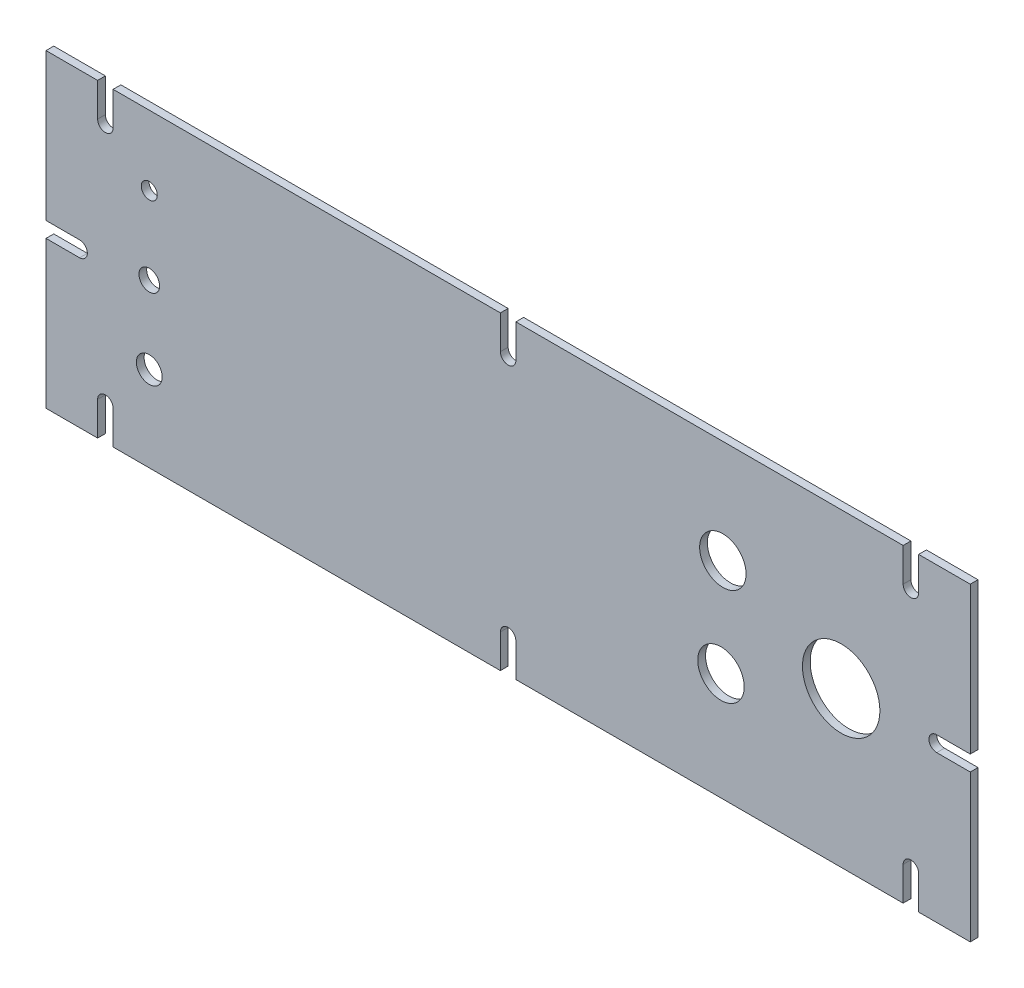
SolidWorks part; units mm, degrees
ref_plane "Front Plane" through (0, 0, 0) normal (0, 0, 1) x (1, 0, 0)
ref_plane "Top Plane" through (0, 0, 0) normal (0, 1, 0) x (1, 0, 0)
ref_plane "Right Plane" through (0, 0, 0) normal (1, 0, 0) x (0, 0, -1)
sketch "Sketch1" plane through (0, 0, 0) normal (0, 0, 1) x (1, 0, 0)
  line L1 (-179, 60) -> (179, 60)
  line L2 (-179, 60) -> (-179, -60)
  line L3 (-179, -60) -> (179, -60)
  line L4 (179, 60) -> (179, -60)
  line L5 (-179, 60) -> (179, -60) construction
  line L6 (-179, -60) -> (179, 60) construction
  point P0 (0, 0)
  dimension "D1" = 120
  dimension "D2" = 358
extrude "Boss-Extrude1" add sketch "Sketch1" along normal blind 3
sketch "Sketch2" plane through (0, 0, 3) normal (0, 0, 1) x (1, 0, 0)
  line L0 (179, 0) -> (88.5, 0) construction
  line L1 (179, -60) -> (179, 60) construction
  circle A0 centre (129, 0) radius 15
  circle A1 centre (83.1742, 20) radius 9
  circle A3 centre (82.4529, -18.2615) radius 9
  point P13 (128.9994, -0.0015)
  dimension "D1" = 30
  dimension "D3" = 18
  dimension "D6" = 2
  dimension "D2" = 50
  dimension "D4" = 20
  dimension "D5" = 50
extrude "Cut-Extrude1" cut sketch "Sketch2" against normal blind 10
sketch "Sketch3" plane through (0, 0, 3) normal (0, 0, 1) x (1, 0, 0)
  line L0 (-179, 60) -> (-179, -60) construction
  line L1 (362, 63) -> (312, 63) construction
  circle A0 centre (-139, 33) radius 3.1
  circle A1 centre (-139, 3) radius 4
  circle A2 centre (-139, -27) radius 5
  dimension "D1" = 6.2
  dimension "D4" = 8
  dimension "D5" = 10
  dimension "D2" = 40
  dimension "D3" = 30
  dimension "D6" = 30
  dimension "D7" = 30
extrude "Cut-Extrude2" cut sketch "Sketch3" against normal blind 10
sketch "Sketch4" plane through (0, 0, 3) normal (0, 0, 1) x (1, 0, 0)
  line L0 (-159, -60) -> (-159, -47)
  line L1 (-179, -60) -> (179, -60) construction
  line L2 (-153, -47) -> (-153, -60)
  line L3 (-179, 60) -> (-179, -60) construction
  line L4 (0, 60) -> (0, -60) construction
  line L5 (0, -60) -> (0, 60) construction
  line L6 (0, 0) -> (37.5832, 0) construction
  line L7 (-153, 47) -> (-153, 60)
  line L8 (-159, 60) -> (-159, 47)
  line L9 (159, 60) -> (159, 47)
  line L10 (153, 47) -> (153, 60)
  line L11 (153, -47) -> (153, -60)
  line L12 (159, -60) -> (159, -47)
  line L13 (-179, 0) -> (179, 0) construction
  line L14 (179, -60) -> (179, 60) construction
  line L15 (-179, 3) -> (-166, 3)
  line L16 (-166, -3) -> (-179, -3)
  line L17 (-3, -60) -> (-3, -47)
  line L18 (3, -47) -> (3, -60)
  line L19 (166, -3) -> (179, -3)
  line L20 (179, 3) -> (166, 3)
  line L21 (3, 47) -> (3, 60)
  line L22 (-3, 60) -> (-3, 47)
  line L23 (-179, 3) -> (-179, -3)
  line L24 (-159, 60) -> (-153, 60)
  line L25 (-3, 60) -> (3, 60)
  line L26 (153, 60) -> (159, 60)
  line L27 (179, 3) -> (179, -3)
  line L28 (153, -60) -> (159, -60)
  line L29 (-3, -60) -> (3, -60)
  line L30 (-159, -60) -> (-153, -60)
  arc A0 (-159, -47) -> (-153, -47) centre (-156, -47) cw
  arc A1 (-159, 47) -> (-153, 47) centre (-156, 47) ccw
  arc A2 (159, 47) -> (153, 47) centre (156, 47) cw
  arc A3 (159, -47) -> (153, -47) centre (156, -47) ccw
  arc A4 (-166, 3) -> (-166, -3) centre (-166, 0) cw
  arc A5 (-3, -47) -> (3, -47) centre (0, -47) cw
  arc A6 (166, 3) -> (166, -3) centre (166, 0) ccw
  arc A7 (-3, 47) -> (3, 47) centre (0, 47) ccw
  dimension "D2" = 3
  dimension "D7" = 3
  dimension "D10" = 3
  dimension "D1" = 6
  dimension "D3" = 13
  dimension "D4" = 20
  dimension "D5" = 3
  dimension "D6" = 3
  dimension "D8" = 13
  dimension "D9" = 13
extrude "Cut-Extrude3" cut sketch "Sketch4" against normal blind 10 contours L9 A2 L10
